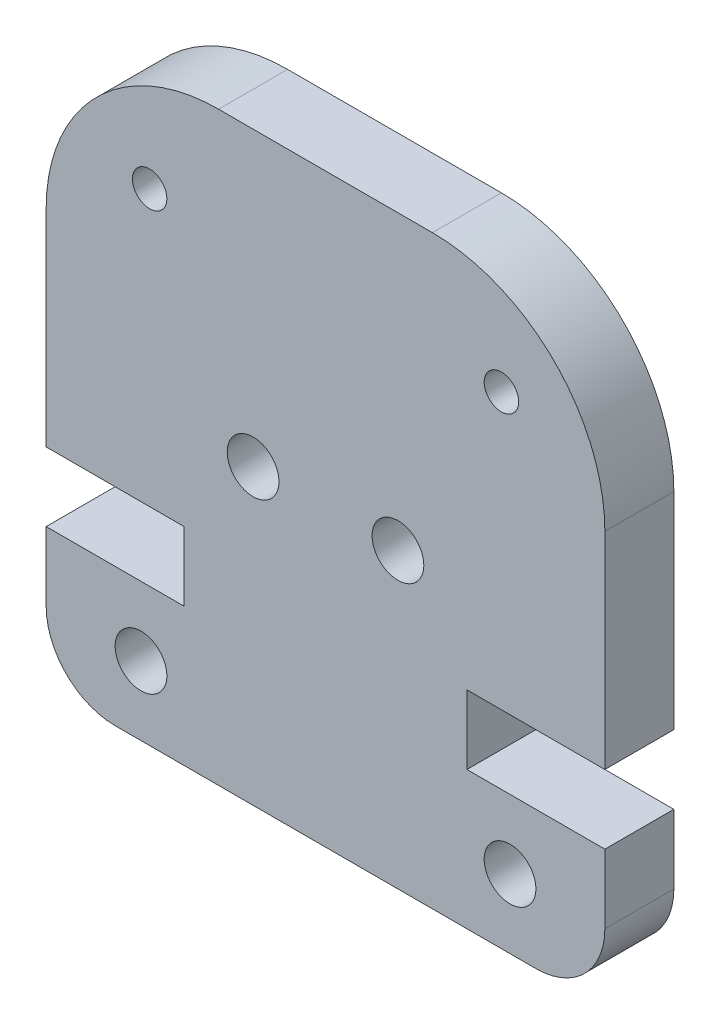
SolidWorks part; units mm, degrees
ref_plane "Front Plane" through (0, 0, 0) normal (0, 0, 1) x (1, 0, 0)
ref_plane "Top Plane" through (0, 0, 0) normal (0, 1, 0) x (1, 0, 0)
ref_plane "Right Plane" through (0, 0, 0) normal (1, 0, 0) x (0, 0, -1)
sketch "Sketch1" plane through (0, 0, 0) normal (0, 0, 1) x (1, 0, 0)
  line L0 (0, 16.98) -> (0, 0) construction
  line L1 (3.1, 16.98) -> (-3.1, 16.98)
  line L2 (6.1, 0) -> (-6.1, 0)
  line L3 (-8.1, 6) -> (-4.1, 6)
  line L4 (-4.1, 6) -> (-4.1, 4)
  line L5 (-4.1, 4) -> (-8.1, 4)
  line L6 (-8.1, 2) -> (-8.1, 4)
  line L7 (8.1, 11.98) -> (8.1, 6)
  line L8 (-8.1, 11.98) -> (-8.1, 6)
  line L24 (8.1, 2) -> (8.1, 4)
  line L27 (4.1, 4) -> (8.1, 4)
  line L30 (4.1, 6) -> (4.1, 4)
  line L31 (8.1, 6) -> (4.1, 6)
  circle A0 centre (-5.35, 2) radius 0.75
  circle A1 centre (-5.1, 13.98) radius 0.5
  arc A2 (-8.1, 11.98) -> (-3.1, 16.98) centre (-3.1, 11.98) cw
  arc A3 (-6.1, 0) -> (-8.1, 2) centre (-6.1, 2) cw
  circle A4 centre (-2.1, 8.5) radius 0.75
  circle A10 centre (2.1, 8.5) radius 0.75
  arc A12 (6.1, 0) -> (8.1, 2) centre (6.1, 2) ccw
  arc A14 (8.1, 11.98) -> (3.1, 16.98) centre (3.1, 11.98) ccw
  circle A16 centre (5.1, 13.98) radius 0.5
  circle A18 centre (5.35, 2) radius 0.75
  dimension "D1" = 1.5
  dimension "D2" = 1
  dimension "D3" = 16.98
  dimension "D4" = 2
  dimension "D5" = 5
  dimension "D6" = 6.1
  dimension "D7" = 3
  dimension "D8" = 3
  dimension "D9" = 6
  dimension "D10" = 8.5
extrude "Boss-Extrude1" add sketch "Sketch1" along normal blind 2
equation "\"D6@Sketch1\"= ( \"fingerWidth@parametersSketch@prostheticParameters.SLDPRT\" - 4 ) / 2'Finger Width - Radius"
equation "\"D3@Sketch1\"= ( \"HL@parametersSketch@prostheticParameters.SLDPRT\" * 0.108 ) - 3 'DIP Legth-Sil. Sh. DIP"
